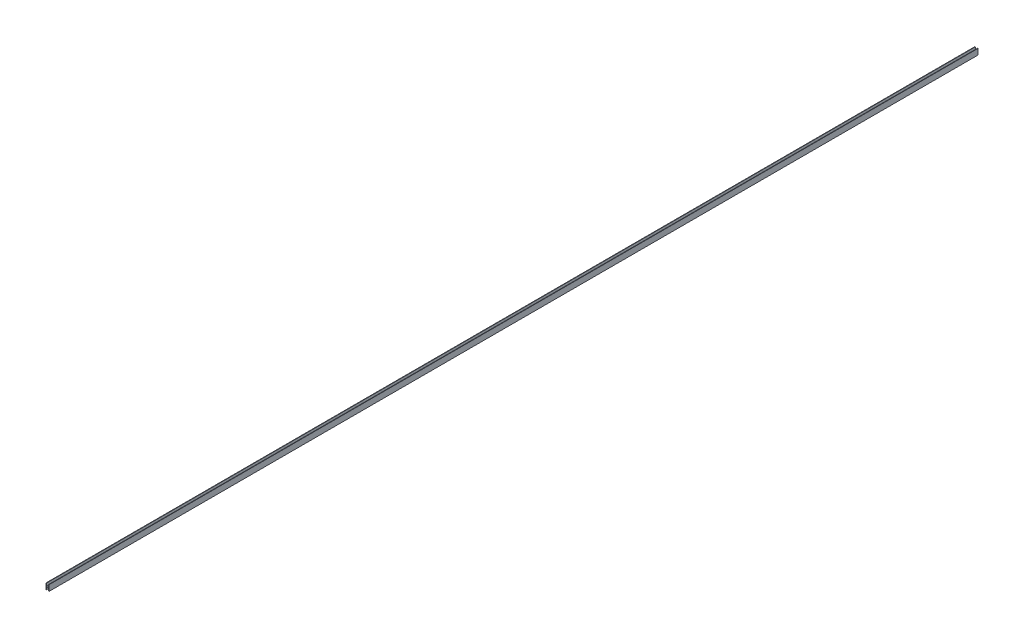
SolidWorks part; units mm, degrees
ref_plane "前视基准面" through (0, 0, 0) normal (0, 0, 1) x (1, 0, 0)
ref_plane "上视基准面" through (0, 0, 0) normal (0, 1, 0) x (1, 0, 0)
ref_plane "右视基准面" through (0, 0, 0) normal (1, 0, 0) x (0, 0, -1)
sketch "草图1" plane through (0, 0, 0) normal (0, 0, 1) x (1, 0, 0)
  line L1 (-4, -7.5) -> (4, -7.5)
  line L2 (-4, -7.5) -> (-4, 7.5)
  line L3 (-4, 7.5) -> (4, 7.5)
  line L4 (4, -7.5) -> (4, 7.5)
  line L5 (-4, -7.5) -> (4, 7.5) construction
  line L6 (-4, 7.5) -> (4, -7.5) construction
  point P0 (0, 0)
  dimension "D1" = 15
  dimension "D2" = 8
extrude "凸台-拉伸1" add sketch "草图1" along normal blind 2400
sketch "草图2" plane through (0, 0, 0) normal (0, 0, -1) x (-1, 0, 0)
  line L0 (4, -7.5) -> (-4, -7.5) construction
  line L1 (-3, -14.5) -> (3, -14.5)
  line L2 (-3, -14.5) -> (-3, -0.5)
  line L3 (-3, -0.5) -> (3, -0.5)
  line L4 (3, -14.5) -> (3, -0.5)
  line L5 (-3, -14.5) -> (3, -0.5) construction
  line L6 (-3, -0.5) -> (3, -14.5) construction
  line L7 (-4, 7.5) -> (4, 7.5) construction
  line L8 (-3, 0.5) -> (3, 0.5)
  line L9 (-3, 0.5) -> (-3, 14.5)
  line L10 (-3, 14.5) -> (3, 14.5)
  line L11 (3, 0.5) -> (3, 14.5)
  line L12 (-3, 0.5) -> (3, 14.5) construction
  line L13 (-3, 14.5) -> (3, 0.5) construction
  point P0 (0, -7.5)
  point P7 (0, 7.5)
  dimension "D1" = 6
  dimension "D2" = 6
  dimension "D3" = 0.5
  dimension "D4" = 0.5
extrude "切除-拉伸1" cut sketch "草图2" against normal blind 2400
